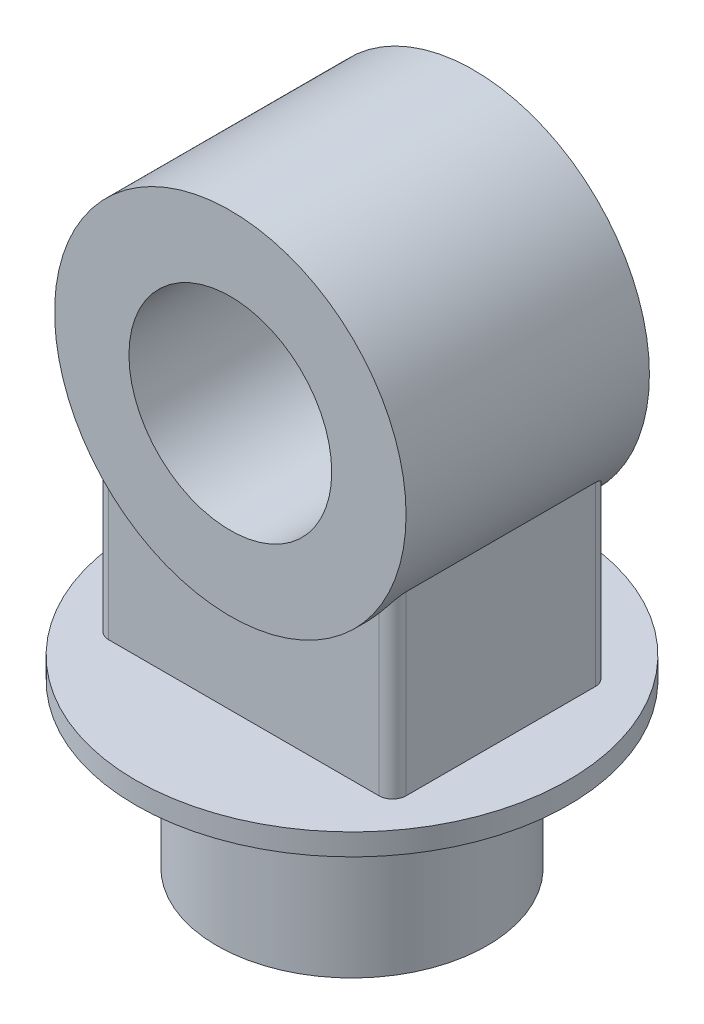
SolidWorks part; units mm, degrees
ref_plane "前视基准面" through (0, 0, 0) normal (0, 0, 1) x (1, 0, 0)
ref_plane "上视基准面" through (0, 0, 0) normal (0, 1, 0) x (1, 0, 0)
ref_plane "右视基准面" through (0, 0, 0) normal (1, 0, 0) x (0, 0, -1)
sketch "草图1" plane through (0, 0, 0) normal (0, 1, 0) x (1, 0, 0)
  circle A0 centre (0, 0) radius 100
  dimension "D1" = 200
extrude "凸台-拉伸1" add sketch "草图1" along normal blind 120
sketch "草图2" plane through (0, 120, 0) normal (0, 1, 0) x (1, 0, 0)
  circle A0 centre (0, 0) radius 160
  dimension "D1" = 320
extrude "凸台-拉伸2" add sketch "草图2" along normal blind 16
sketch "草图3" plane through (0, 0, 0) normal (0, 0, 1) x (1, 0, 0)
  line L0 (160, 136) -> (-160, 136) construction
  circle A0 centre (0, 336) radius 75
  circle A1 centre (0, 336) radius 130
  dimension "D1" = 150
  dimension "D2" = 260
  dimension "D3" = 200
extrude "凸台-拉伸3" add sketch "草图3" along normal mid plane 180 separate body
sketch "草图4" plane through (0, 136, 0) normal (0, 1, 0) x (1, 0, 0)
  line L1 (-110, 80) -> (110, 80)
  line L2 (-110, 80) -> (-110, -80)
  line L3 (-110, -80) -> (110, -80)
  line L4 (110, 80) -> (110, -80)
  line L5 (-110, 80) -> (110, -80) construction
  line L6 (-110, -80) -> (110, 80) construction
  point P0 (0, 0)
  dimension "D1" = 160
  dimension "D2" = 220
extrude "凸台-拉伸4" add sketch "草图4" along normal up to next
fillet "圆角1" radius 10 4 edges at (-110, 201.359, 80) (-110, 201.359, -80) (110, 201.359, -80) (110, 201.359, 80)
